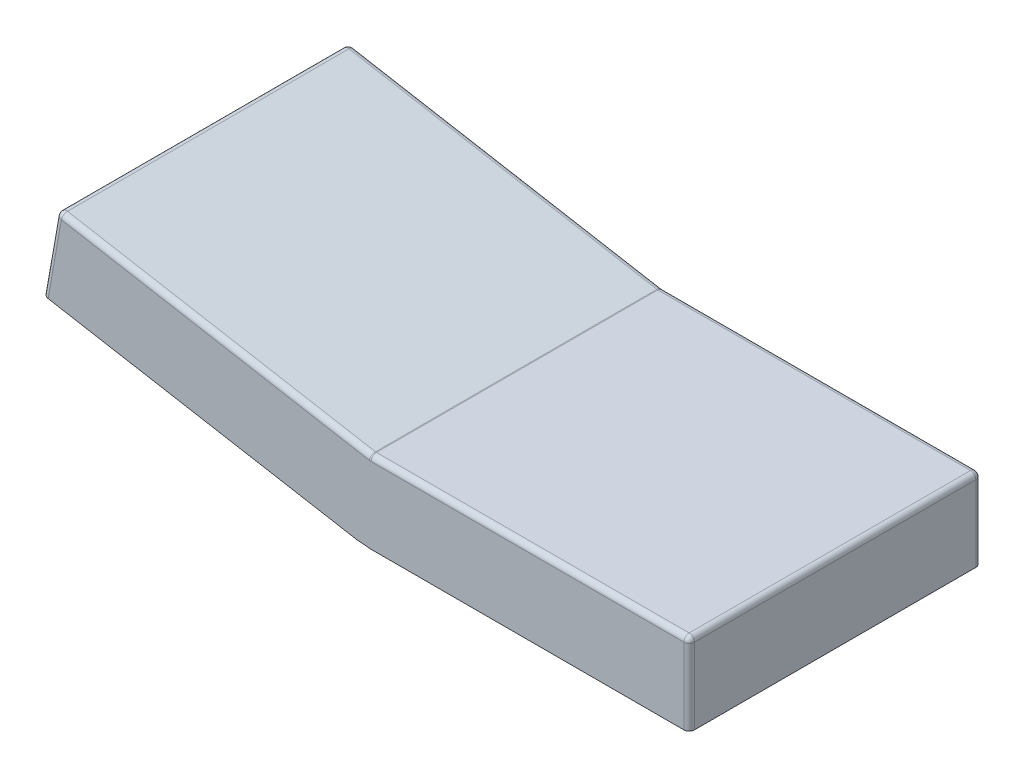
SolidWorks part; units mm, degrees
ref_plane "Front" through (0, 0, 0) normal (0, 0, 1) x (1, 0, 0)
ref_plane "Top" through (0, 0, 0) normal (0, 1, 0) x (1, 0, 0)
ref_plane "Right" through (0, 0, 0) normal (1, 0, 0) x (0, 0, -1)
sketch "Sketch1" plane through (0, 0, 0) normal (0, 0, 1) x (1, 0, 0)
  line L0 (0, 0) -> (-30, 0)
  line L1 (-30, 0) -> (-59.5442, 5.2094)
  line L2 (-59.5442, 5.2094) -> (-60.8739, -2.3317)
  line L3 (-30, 0) -> (-31.3297, -7.5412)
  line L4 (-30, 0) -> (-30, -7.6575)
  line L5 (0, 0) -> (0, -7.6575)
  line L6 (0, -7.6575) -> (-30, -7.6575)
  line L7 (-60.8739, -2.3317) -> (-31.3297, -7.5412)
  line L8 (-30, -7.6575) -> (-31.3297, -7.5412)
  dimension "D1" = 170
  dimension "D2" = 30
extrude "Boss-Extrude1" add sketch "Sketch1" along normal blind 27.5 contours L2 L7 L3 L1 | L8 L4 L3 | L6 L5 L0 L4
fillet "Fillet1" radius 0.5 11 edges at (-30, 0, 13.75) (0, 0, 13.75) (0, -3.8288, 0) (0, -3.8288, 27.5) (-15, 0, 0) (-15, 0, 27.5) (-60.2091, 1.4389, 0) (-60.2091, 1.4389, 27.5) (-44.7721, 2.6047, 0) (-44.7721, 2.6047, 27.5) (-59.5442, 5.2094, 13.75)
